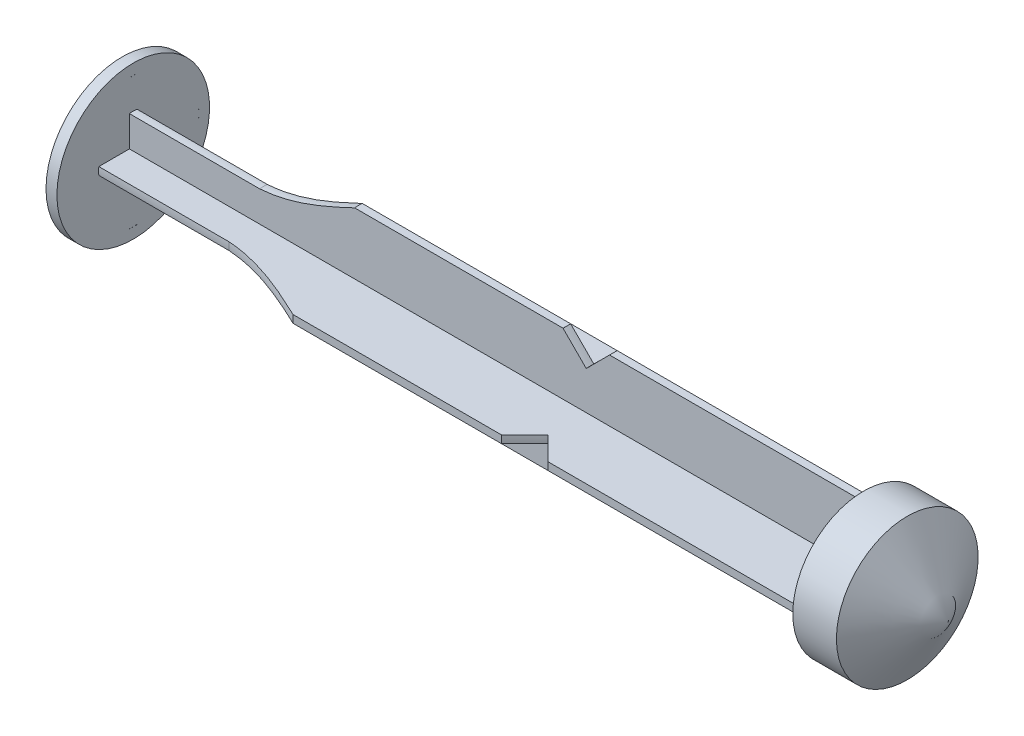
SolidWorks part; units mm, degrees
material "Акрил (Средняя-высокая ударопрочность)"
ref_plane "Спереди" through (0, 0, 0) normal (0, 0, 1) x (1, 0, 0)
ref_plane "Сверху" through (0, 0, 0) normal (0, 1, 0) x (1, 0, 0)
ref_plane "Справа" through (0, 0, 0) normal (1, 0, 0) x (0, 0, -1)
other "Configuration Table"
sketch "Эскиз1" plane through (0, 0, 0) normal (1, 0, 0) x (0, 0, -1)
  line L0 (-6, 0.35) -> (-0.35, 0.35)
  line L1 (-0.35, 0.35) -> (-0.35, 6)
  line L2 (-0.35, 6) -> (0.35, 6)
  line L3 (0.35, 6) -> (0.35, 0.35)
  line L4 (0.35, 0.35) -> (6, 0.35)
  line L5 (6, 0.35) -> (6, -0.35)
  line L6 (6, -0.35) -> (0.35, -0.35)
  line L7 (0.35, -0.35) -> (0.35, -6)
  line L8 (0.35, -6) -> (-0.35, -6)
  line L9 (-0.35, -6) -> (-0.35, -0.35)
  line L10 (-0.35, -0.35) -> (-6, -0.35)
  line L11 (-6, -0.35) -> (-6, 0.35)
  dimension "D1" = 0.7
  dimension "D2" = 0.7
  dimension "D3" = 0.7
  dimension "D4" = 6
  dimension "D5" = 6
  dimension "D6" = 6
extrude "Бобышка-Вытянуть1" add sketch "Эскиз1" along normal blind 67
sketch "Эскиз2" plane through (67, 0, 0) normal (1, 0, 0) x (0, 0, -1)
  circle A0 centre (0, 0) radius 6.25
  dimension "D1" = 12.5
sketch "Эскиз3" plane through (0, 0, 0) normal (0, 0, 1) x (1, 0, 0)
  line L1 (67, -6.25) -> (67, 6.25) construction
  line L4 (74.7528, 0) -> (71, 6.5)
  line L5 (71, 6.5) -> (67, 6.5)
  line L7 (0, 7) -> (-1, 7)
  line L10 (-1, 7) -> (-1, 0)
  line L11 (-1, 0) -> (0, 0)
  line L12 (0, 0) -> (80.7186, 0) construction
  line L13 (0, 7) -> (0, 0)
  line L16 (67, 6.5) -> (67, 0)
  line L17 (67, 0) -> (74.7528, 0)
  dimension "D1" = 6.5
  dimension "D3" = 4
  dimension "D4" = 120
revolve "Повернуть1" add sketch "Эскиз3" angle 360 about L12
sketch "Эскиз4" plane through (0, 0, 0) normal (0, 0, 1) x (1, 0, 0)
  line L0 (0, 6) -> (0, 3.175)
  line L1 (0, 6) -> (0, 0.35) construction
  line L2 (0, 3.175) -> (11.9533, 3.175)
  line L3 (39.7801, 8.5576) -> (39.7801, 6)
  line L4 (67, 6) -> (0, 6) construction
  line L5 (39.7801, 6) -> (41.9043, 3.8758)
  line L6 (41.9043, 3.8758) -> (45.0763, 7.0478)
  line L7 (45.0763, 7.0478) -> (24.9964, 20.7837)
  line L8 (24.9964, 20.7837) -> (10.9135, 15.6056)
  line L9 (10.9135, 15.6056) -> (0, 6)
  line L10 (0, 0) -> (120.9596, 0) construction
  spline S0 degree 3 poles (11.9533, 3.175) (13.8256, 3.302) (23.0445, 6.1336) (30.6965, 12.6119) (39.7801, 8.5576) knots 0 0 0 0 0.195436 1 1 1 1
  dimension "D1" = 45
  dimension "D2" = 45
revolve "Вырез-Повернуть1" cut sketch "Эскиз4" angle 360 about L10
sketch "Эскиз5" plane through (0, 0, 0) normal (0, 0, 1) x (1, 0, 0)
  point P0 (74.7528, 0)
